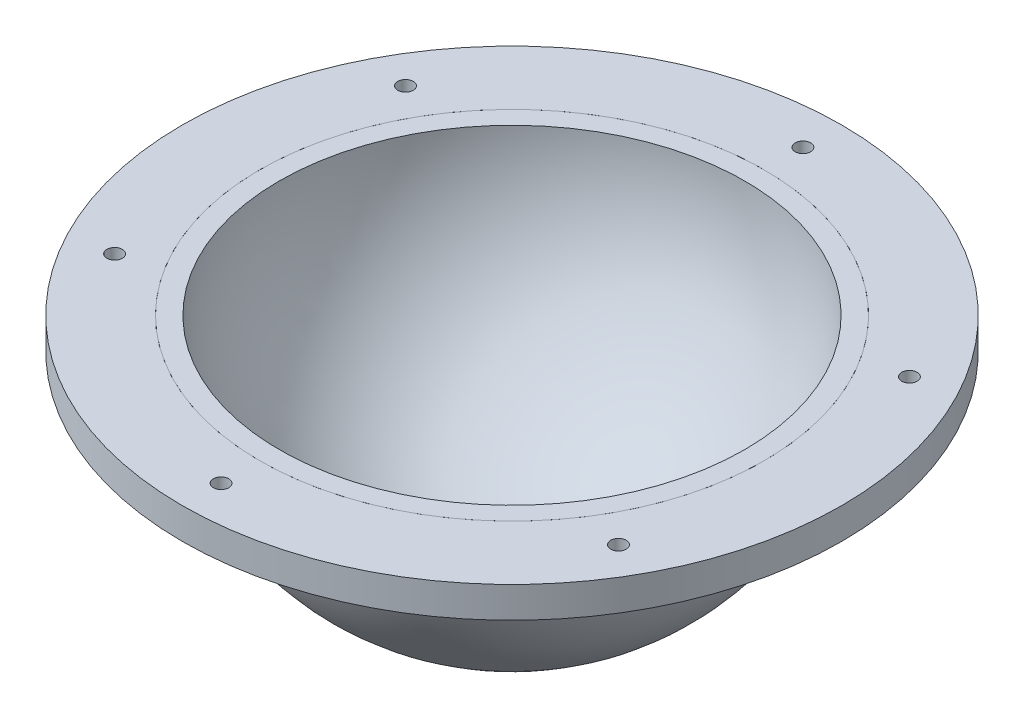
SolidWorks part; units mm, degrees
ref_plane "前视基准面" through (0, 0, 0) normal (0, 0, 1) x (1, 0, 0)
ref_plane "上视基准面" through (0, 0, 0) normal (0, 1, 0) x (1, 0, 0)
ref_plane "右视基准面" through (0, 0, 0) normal (1, 0, 0) x (0, 0, -1)
sketch "草图1" plane through (0, 0, 0) normal (0, 1, 0) x (1, 0, 0)
  line L1 (0, -65) -> (0, 65) construction
  arc A0 (0, -65) -> (0, 65) centre (0, 0) ccw
revolve "旋转-薄壁14" add sketch "草图1" angle 180 about L1 wall 5
sketch "草图3" plane through (0, 0, 0) normal (0, 1, 0) x (1, 0, 0)
  circle A0 centre (0, 0) radius 85
  circle A1 centre (0, 0) radius 65
extrude "凸台-拉伸1" add sketch "草图3" against normal blind 8 separate body
sketch "草图4" plane through (0, 0, 0) normal (0, 1, 0) x (1, 0, 0)
  line L0 (0, 85) -> (0, 75) construction
  circle A0 centre (0, 0) radius 85 construction
  circle A1 centre (0, 75) radius 2
  circle A2 centre (64.9519, 37.5) radius 2
  circle A3 centre (64.9519, -37.5) radius 2
  circle A4 centre (0, -75) radius 2
  circle A5 centre (-64.9519, -37.5) radius 2
  circle A6 centre (-64.9519, 37.5) radius 2
  point P18 (0, 0)
  dimension "D1" = 6
extrude "切除-拉伸2" cut sketch "草图4" against normal through all contours A5 | A4 | A3 | A2 | A1 | A6
